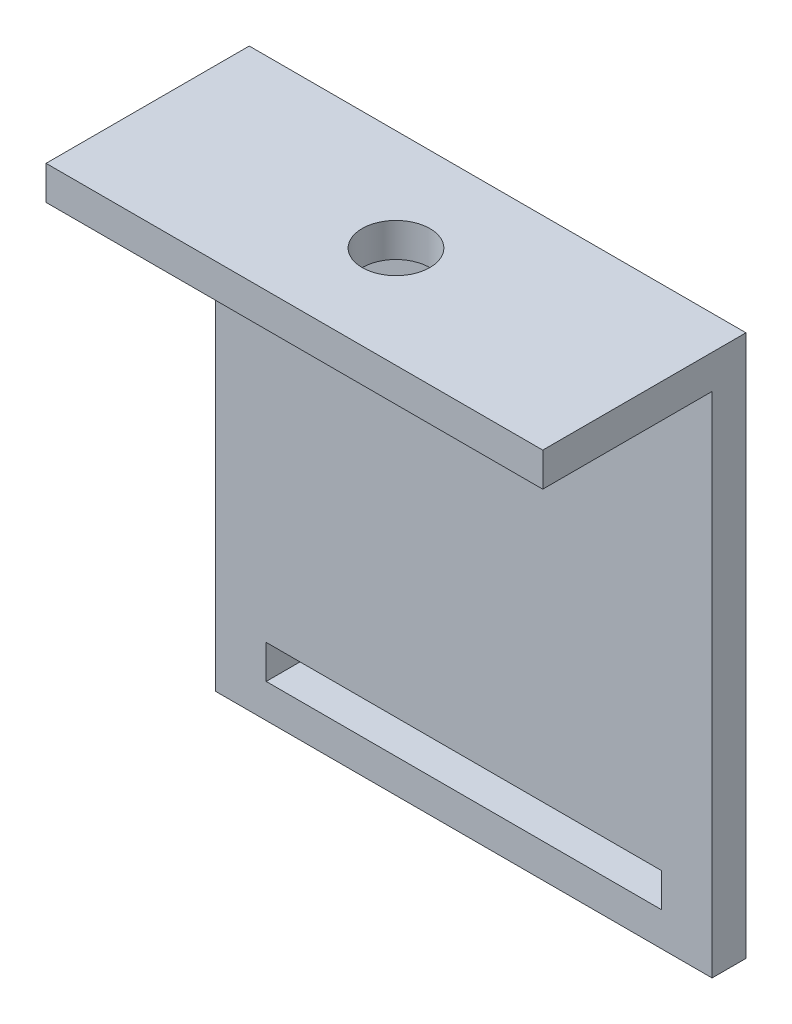
SolidWorks part; units mm, degrees
ref_plane "Piano frontale" through (0, 0, 0) normal (0, 0, 1) x (1, 0, 0)
ref_plane "Piano superiore" through (0, 0, 0) normal (0, 1, 0) x (1, 0, 0)
ref_plane "Piano destro" through (0, 0, 0) normal (1, 0, 0) x (0, 0, -1)
sketch "Schizzo8" plane through (0, 0, 0) normal (1, 0, 0) x (0, 0, -1)
  line L0 (0, 0) -> (0, 3)
  line L1 (0, 3) -> (18, 3)
  line L2 (18, 3) -> (18, -45)
  line L3 (18, -45) -> (15, -45)
  line L4 (15, -45) -> (15, 0)
  line L5 (15, 0) -> (0, 0)
  dimension "D1" = 3
  dimension "D2" = 18
  dimension "D3" = 45
  dimension "D4" = 3
extrude "Estrusione-Estrusione6" add sketch "Schizzo8" along normal blind 44
sketch "Schizzo9" plane through (0, 0, -15) normal (0, 0, 1) x (1, 0, 0)
  line L0 (44, -45) -> (0, -45) construction
  line L1 (4.5, -42) -> (39.5, -42)
  line L2 (4.5, -42) -> (4.5, -39)
  line L3 (4.5, -39) -> (39.5, -39)
  line L4 (39.5, -42) -> (39.5, -39)
  line L5 (0, 0) -> (0, -45) construction
  dimension "D1" = 3
  dimension "D2" = 35
  dimension "D3" = 3
  dimension "D4" = 4.5
extrude "Taglio-Estrusione2" cut sketch "Schizzo9" against normal blind 44
sketch "Schizzo10" plane through (0, 3, 0) normal (0, 1, 0) x (1, 0, 0)
  line L0 (0, 18) -> (44, 0) construction
  line L1 (44, 18) -> (44, 0) construction
  line L2 (44, 0) -> (44, 18) construction
  line L3 (44, 18) -> (0, 0) construction
  circle A0 centre (22, 9) radius 3
  dimension "D1" = 6
extrude "Taglio-Estrusione3" cut sketch "Schizzo10" against normal blind 10
